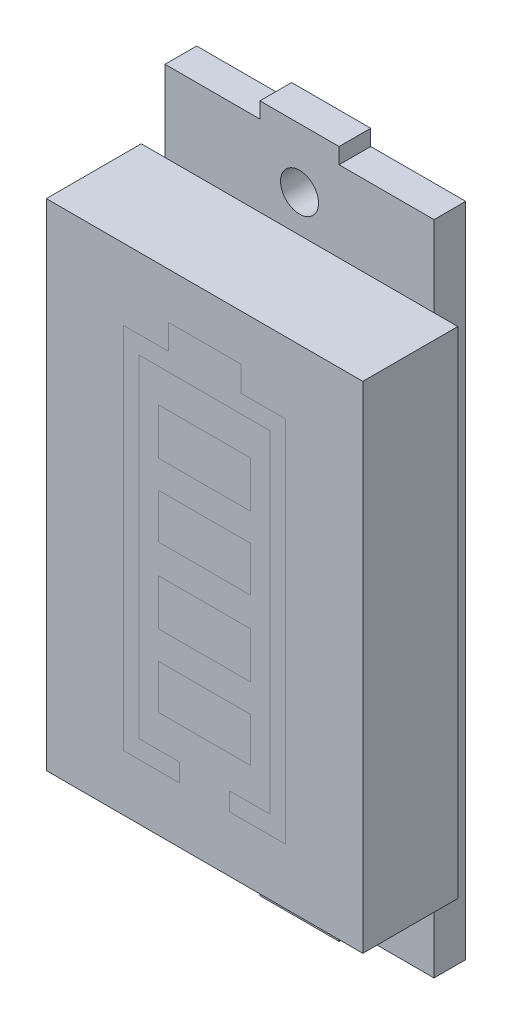
SolidWorks part; units mm, degrees
ref_plane "Front Plane" through (0, 0, 0) normal (0, 0, 1) x (1, 0, 0)
ref_plane "Top Plane" through (0, 0, 0) normal (0, 1, 0) x (1, 0, 0)
ref_plane "Right Plane" through (0, 0, 0) normal (1, 0, 0) x (0, 0, -1)
sketch "Sketch1" plane through (0, 0, 0) normal (0, 0, 1) x (1, 0, 0)
  line L1 (-10, -15.65) -> (10, -15.65)
  line L2 (-10, -15.65) -> (-10, 15.65)
  line L3 (-10, 15.65) -> (10, 15.65)
  line L4 (10, -15.65) -> (10, 15.65)
  line L5 (-10, -15.65) -> (10, 15.65) construction
  line L6 (-10, 15.65) -> (10, -15.65) construction
  point P0 (0, 0)
  dimension "D1" = 31.3
  dimension "D2" = 20
extrude "Boss-Extrude1" add sketch "Sketch1" along normal blind 6
sketch "Sketch2" plane through (0, 0, 0) normal (0, 0, -1) x (-1, 0, 0)
  line L1 (-8.5, -20.75) -> (8.5, -20.75)
  line L2 (-8.5, -20.75) -> (-8.5, 20.75)
  line L3 (-8.5, 20.75) -> (8.5, 20.75)
  line L4 (8.5, -20.75) -> (8.5, 20.75)
  line L5 (-8.5, -20.75) -> (8.5, 20.75) construction
  line L6 (-8.5, 20.75) -> (8.5, -20.75) construction
  point P0 (0, 0)
  dimension "D1" = 41.5
  dimension "D2" = 17
extrude "Boss-Extrude2" add sketch "Sketch2" along normal blind 2
sketch "Sketch3" plane through (0, 0, -2) normal (0, 0, -1) x (-1, 0, 0)
  line L1 (-2.5, -21.75) -> (2.5, -21.75)
  line L2 (-2.5, -21.75) -> (-2.5, 21.75)
  line L3 (-2.5, 21.75) -> (2.5, 21.75)
  line L4 (2.5, -21.75) -> (2.5, 21.75)
  line L5 (-2.5, -21.75) -> (2.5, 21.75) construction
  line L6 (-2.5, 21.75) -> (2.5, -21.75) construction
  point P0 (0, 0)
  dimension "D1" = 5
  dimension "D2" = 43.5
extrude "Boss-Extrude3" add sketch "Sketch3" against normal blind 2
hole_wizard "M2 Clearance Hole1" positions "Sketch7" profile "Sketch6" hole size "M2" standard "ISO" end condition up to next
sketch "Sketch7" plane through (0, 0, -2) normal (0, 0, -1) x (-1, 0, 0)
  line L0 (0, 18) -> (0, -18) construction
  point P0 (0, 18)
  point P2 (0, -18)
  dimension "D1" = 36
sketch "Sketch6" plane through (0, 18, -2) normal (1, 0, 0) x (0, 1, 0)
  line L0 (0, 0) -> (0, 2)
  line L1 (0, 2) -> (1.2, 2)
  line L2 (1.2, 2) -> (1.2, 0)
  line L5 (1.2, 0) -> (0, 0)
  line L11 (0, -6.35) -> (0, 107.95) construction
  dimension "Thru Hole Dia." = 2.4
  dimension "Thru Hole Depth" = 2
sketch "Sketch8" plane through (0, 0, 6) normal (0, 0, 1) x (1, 0, 0)
  line L0 (-9.1718, 18.8198) -> (22.1282, 18.8198) construction
  line L1 (0, -21.75) -> (0, 21.75) construction
  line L2 (2.5, -21.75) -> (-2.5, -21.75) construction
  line L3 (-2.5, 21.75) -> (2.5, 21.75) construction
  line L4 (-1.5877, -12.1184) -> (-5.119, -12.1184)
  line L5 (-5.119, -12.1184) -> (-5.119, 11.1491)
  line L6 (-5.119, 11.1491) -> (-2.2936, 11.1491)
  line L7 (-2.2936, 11.1491) -> (-2.2936, 12.739)
  line L8 (-2.2936, 12.739) -> (2.2936, 12.739)
  line L10 (4.1285, 10.0169) -> (-4.1285, 10.0169)
  line L11 (-4.1285, 10.0169) -> (-4.1285, -10.9726)
  line L12 (-4.1285, -10.9726) -> (-1.5877, -10.9726)
  line L13 (-1.5877, -10.9726) -> (-1.5877, -12.1184)
  line L14 (2.9107, -8.9213) -> (-2.9107, -8.9213)
  line L15 (-2.9107, -8.9213) -> (-2.9107, -6.1253)
  line L16 (-2.9107, -6.1253) -> (2.9107, -6.1253)
  line L17 (2.9107, -4.3502) -> (-2.9107, -4.3502)
  line L18 (-2.9107, -4.3502) -> (-2.9107, -1.4409)
  line L19 (-2.9107, -1.4409) -> (2.9107, -1.4409)
  line L20 (2.9107, 0.4013) -> (-2.9107, 0.4013)
  line L21 (-2.9107, 0.4013) -> (-2.9107, 3.2342)
  line L22 (-2.9107, 3.2342) -> (2.9107, 3.2342)
  line L23 (2.9107, 4.9905) -> (-2.9107, 4.9905)
  line L24 (-2.9107, 4.9905) -> (-2.9107, 7.9067)
  line L25 (-2.9107, 7.9067) -> (2.9107, 7.9067)
  line L26 (2.9107, 4.9905) -> (2.9107, 7.9067)
  line L27 (2.9107, 0.4013) -> (2.9107, 3.2342)
  line L28 (2.9107, -4.3502) -> (2.9107, -1.4409)
  line L29 (2.9107, -8.9213) -> (2.9107, -6.1253)
  line L30 (1.5877, -10.9726) -> (1.5877, -12.1184)
  line L31 (4.1285, -10.9726) -> (1.5877, -10.9726)
  line L32 (4.1285, 10.0169) -> (4.1285, -10.9726)
  line L33 (2.2936, 11.1491) -> (2.2936, 12.739)
  line L34 (5.119, 11.1491) -> (2.2936, 11.1491)
  line L35 (5.119, -12.1184) -> (5.119, 11.1491)
  line L36 (1.5877, -12.1184) -> (5.119, -12.1184)
  point P35 (0, 7.9067)
  point P36 (0, 4.9905)
  point P37 (0, 3.2342)
  point P38 (0, 0.4013)
  point P39 (0, -1.4409)
  point P40 (0, -4.3502)
  point P41 (0, -6.1253)
  point P42 (0, -8.9213)
  point P46 (0, 10.0169)
  point P47 (0, 12.739)
  dimension "D1" = 31.3
split line "Split Line1"
